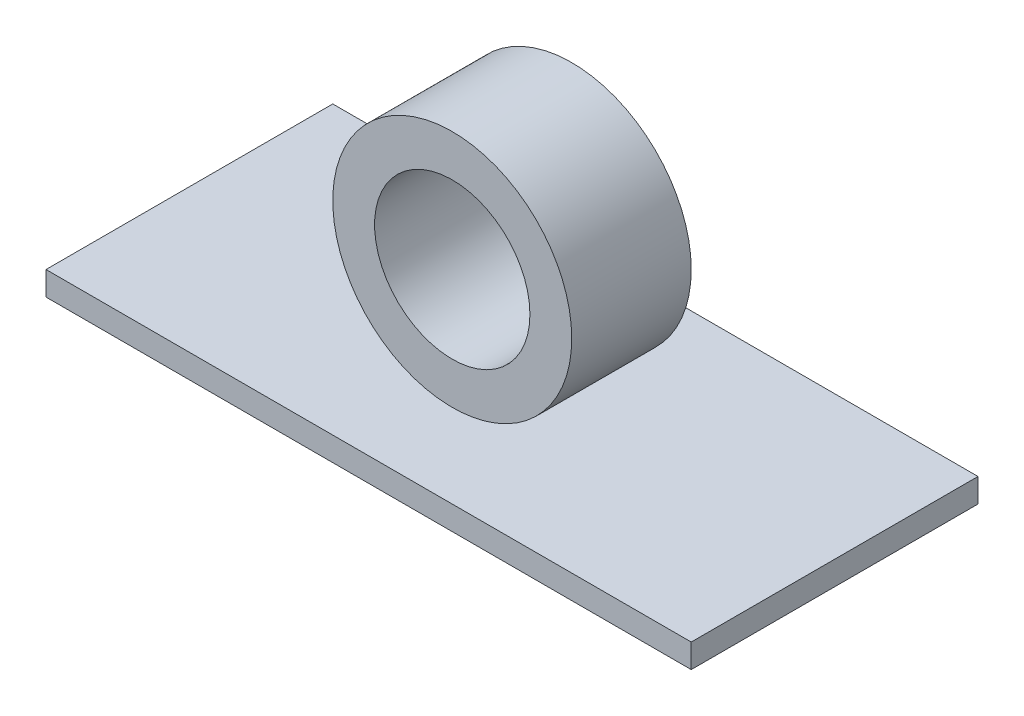
SolidWorks part; units mm, degrees
ref_plane "Front Plane" through (0, 0, 0) normal (0, 0, 1) x (1, 0, 0)
ref_plane "Top Plane" through (0, 0, 0) normal (0, 1, 0) x (1, 0, 0)
ref_plane "Right Plane" through (0, 0, 0) normal (1, 0, 0) x (0, 0, -1)
sketch "Sketch1" plane through (0, 0, 0) normal (0, 1, 0) x (1, 0, 0)
  line L1 (-27, -12) -> (27, -12)
  line L2 (-27, -12) -> (-27, 12)
  line L3 (-27, 12) -> (27, 12)
  line L4 (27, -12) -> (27, 12)
  line L5 (-27, -12) -> (27, 12) construction
  line L6 (-27, 12) -> (27, -12) construction
  point P0 (0, 0)
  dimension "D1" = 54
  dimension "D2" = 24
extrude "Boss-Extrude1" add sketch "Sketch1" along normal blind 2
sketch "Sketch2" plane through (0, 0, 0) normal (0, 0, 1) x (1, 0, 0)
  line L0 (-27, 2) -> (27, 2) construction
  circle A0 centre (0, 12) radius 10
  circle A1 centre (0, 12) radius 6.5
  dimension "D1" = 20
  dimension "D2" = 13
extrude "Boss-Extrude2" add sketch "Sketch2" along normal mid plane 10 separate body
